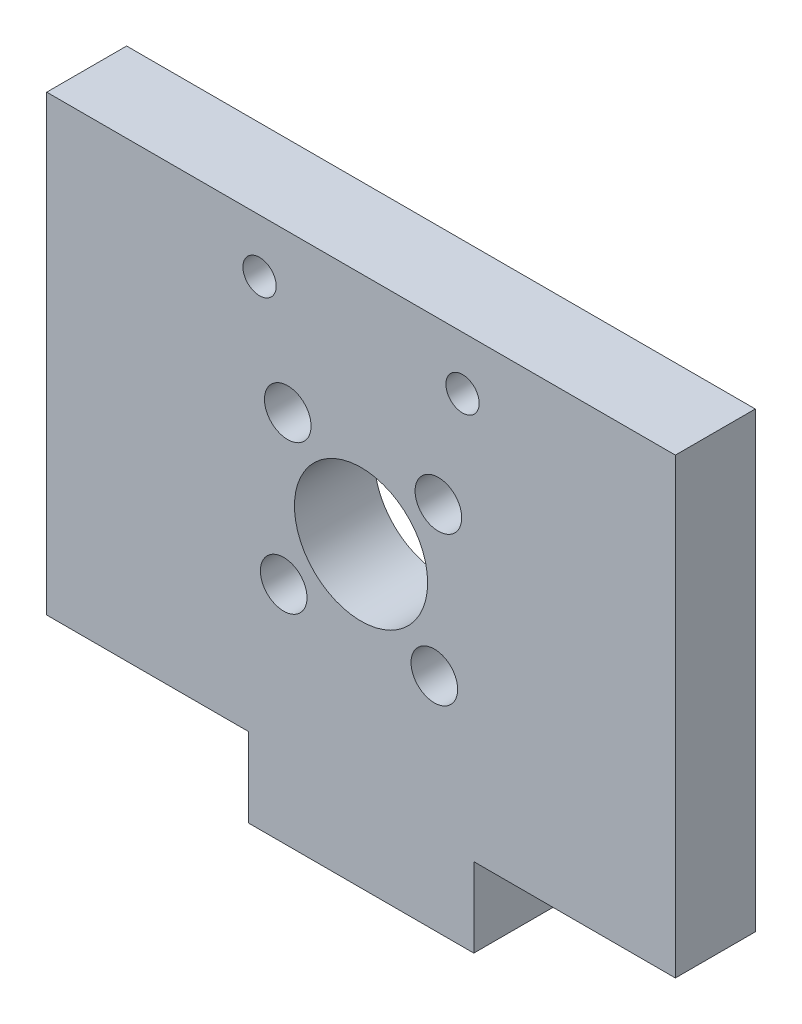
SolidWorks part; units mm, degrees
ref_plane "Front" through (0, 0, 0) normal (0, 0, 1) x (1, 0, 0)
ref_plane "Top" through (0, 0, 0) normal (0, 1, 0) x (1, 0, 0)
ref_plane "Right" through (0, 0, 0) normal (1, 0, 0) x (0, 0, -1)
sketch "Sketch1" plane through (0, 0, 0) normal (0, 0, 1) x (1, 0, 0)
  line L0 (348.9169, 226.9985) -> (348.9169, 260.9985)
  line L1 (348.9169, 260.9985) -> (301.7169, 260.9985)
  line L2 (301.7169, 260.9985) -> (301.7169, 226.9985)
  line L3 (301.7169, 226.9985) -> (316.8503, 226.9985)
  line L4 (316.8503, 226.9985) -> (316.8503, 221.0491)
  line L6 (316.8503, 221.0491) -> (333.7836, 221.0491)
  line L8 (333.7836, 221.0491) -> (333.7836, 226.9985)
  line L9 (333.7836, 226.9985) -> (348.9169, 226.9985)
  circle A0 centre (325.3169, 243.3985) radius 5
  circle A1 centre (331.1239, 248.9011) radius 1.75
  circle A2 centre (319.8143, 249.2055) radius 1.75
  circle A3 centre (319.5099, 237.8959) radius 1.75
  circle A4 centre (330.8195, 237.5915) radius 1.75
  dimension "D1" = 39.9494
  dimension "D2" = 34
extrude "Boss-Extrude1" add sketch "Sketch1" along normal blind 6
sketch "Sketch2" plane through (0, 0, 6) normal (0, 0, 1) x (1, 0, 0)
  line L0 (301.7169, 256.9985) -> (348.9169, 256.9985) construction
  line L1 (301.7169, 260.9985) -> (301.7169, 226.9985) construction
  line L2 (348.9169, 226.9985) -> (348.9169, 260.9985) construction
  line L3 (348.9169, 260.9985) -> (301.7169, 260.9985) construction
  circle A0 centre (317.6969, 256.9985) radius 1.25
  circle A1 centre (332.9369, 256.9985) radius 1.25
  point P10 (325.3169, 256.9985)
  dimension "D1" = 2.5
  dimension "D2" = 15.24
  dimension "D3" = 7.62
  dimension "D4" = 4
extrude "Cut-Extrude1" cut sketch "Sketch2" against normal up to next
